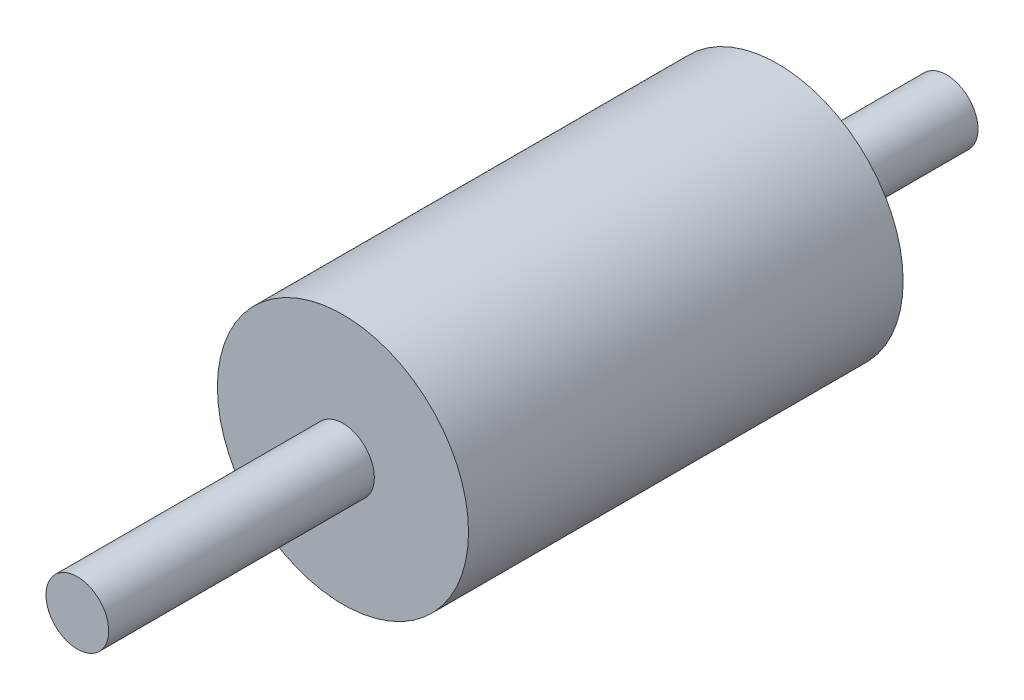
SolidWorks part; units mm, degrees
ref_plane "Спереди" through (0, 0, 0) normal (0, 0, 1) x (1, 0, 0)
ref_plane "Сверху" through (0, 0, 0) normal (0, 1, 0) x (1, 0, 0)
ref_plane "Справа" through (0, 0, 0) normal (1, 0, 0) x (0, 0, -1)
sketch "Эскиз1" plane through (0, 0, 0) normal (0, 0, 1) x (1, 0, 0)
  circle A0 centre (0, 0) radius 0.65
  dimension "D1" = 1.3
extrude "Бобышка-Вытянуть1" add sketch "Эскиз1" along normal blind 10 and the other way blind 8
sketch "Эскиз2" plane through (0, 0, 0) normal (0, 0, 1) x (1, 0, 0)
  circle A0 centre (0, 0) radius 2.6
  dimension "D1" = 5.2
extrude "Бобышка-Вытянуть3" add sketch "Эскиз2" along normal blind 4.5 and the other way blind 4.5 contours A0
